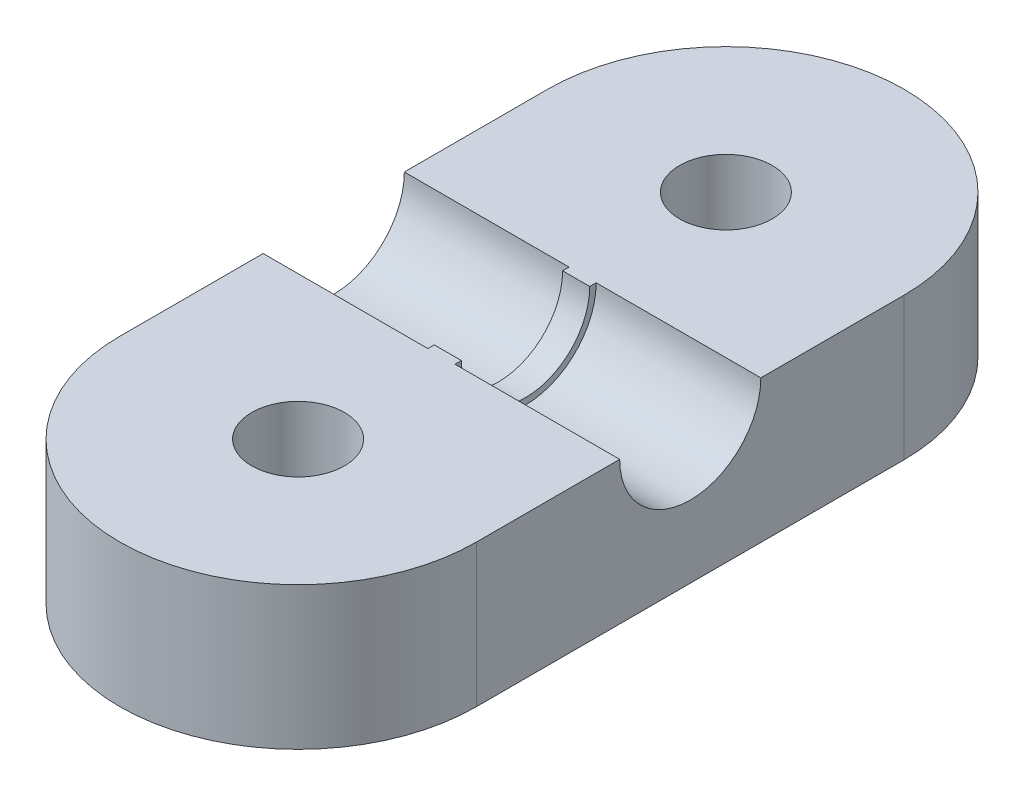
SolidWorks part; units mm, degrees
ref_plane "Front Plane" through (0, 0, 0) normal (0, 0, 1) x (1, 0, 0)
ref_plane "Top Plane" through (0, 0, 0) normal (0, 1, 0) x (1, 0, 0)
ref_plane "Right Plane" through (0, 0, 0) normal (1, 0, 0) x (0, 0, -1)
sketch "Sketch1" plane through (0, 0, 0) normal (0, 1, 0) x (1, 0, 0)
  line L0 (0, 27.5) -> (0, -27.5) construction
  line L1 (-12.5, 27.5) -> (12.5, 27.5)
  line L2 (-12.5, 27.5) -> (-12.5, -27.5)
  line L3 (-12.5, -27.5) -> (12.5, -27.5)
  line L4 (12.5, 27.5) -> (12.5, -27.5)
  line L5 (-12.5, 27.5) -> (12.5, -27.5) construction
  line L6 (-12.5, -27.5) -> (12.5, 27.5) construction
  line L7 (-12.5, 0) -> (12.5, 0) construction
  circle A0 centre (0, 15) radius 3.25
  circle A1 centre (0, -15) radius 3.25
  circle A2 centre (0, 15) radius 12.5
  circle A3 centre (0, -15) radius 12.5
  point P0 (0, 0)
  dimension "D3" = 6.5
  dimension "D1" = 25
  dimension "D4" = 30
extrude "Boss-Extrude1" add sketch "Sketch1" along normal blind 10 contours L2 A3 L4 A2 | A2 A0 | A3 A1
sketch "Sketch2" plane through (12.5, 0, 0) normal (1, 0, 0) x (0, 0, -1)
  line L1 (15, 10) -> (-15, 10) construction
  circle A0 centre (0, 10) radius 4.95
  dimension "D1" = 9.9
extrude "Cut-Extrude1" cut sketch "Sketch2" against normal up to next
sketch "Sketch3" plane through (0, 0, 0) normal (1, 0, 0) x (0, 0, -1)
  line L0 (-4.95, 10) -> (4.95, 10)
  arc A0 (-4.95, 10) -> (4.95, 10) centre (0, 10) ccw construction
  arc A1 (-4.95, 10) -> (4.95, 10) centre (0, 10) ccw
  circle A2 centre (0, 10) radius 4.5
  dimension "D1" = 9
extrude "Boss-Extrude2" add sketch "Sketch3" along normal mid plane 1.9 contours A2 L0 A1
